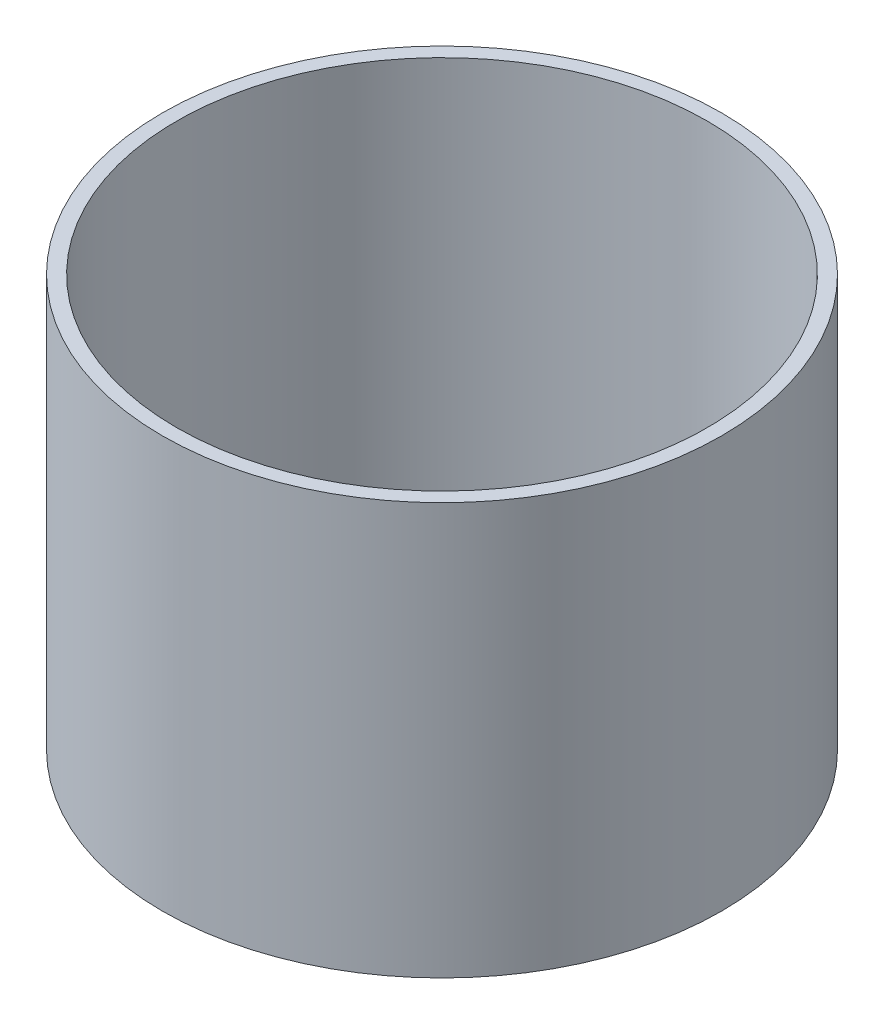
SolidWorks part; units mm, degrees
material "Acrylic (Medium-high impact)"
ref_plane "Front Plane" through (0, 0, 0) normal (0, 0, 1) x (1, 0, 0)
ref_plane "Top Plane" through (0, 0, 0) normal (0, 1, 0) x (1, 0, 0)
ref_plane "Right Plane" through (0, 0, 0) normal (1, 0, 0) x (0, 0, -1)
sketch "Sketch1" plane through (0, 0, 0) normal (0, 1, 0) x (1, 0, 0)
  circle A0 centre (0, 0) radius 93.6625
  circle A1 centre (0, 0) radius 88.9
  dimension "D1" = 187.325
  dimension "D2" = 177.8
extrude "Boss-Extrude1" add sketch "Sketch1" along normal mid plane 137.8509
